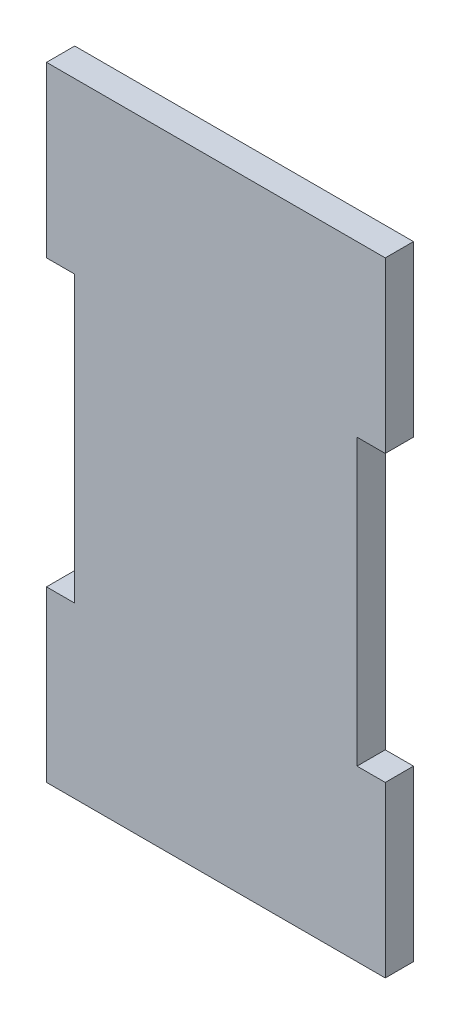
SolidWorks part; units mm, degrees
ref_plane "Front Plane" through (0, 0, 0) normal (0, 0, 1) x (1, 0, 0)
ref_plane "Top Plane" through (0, 0, 0) normal (0, 1, 0) x (1, 0, 0)
ref_plane "Right Plane" through (0, 0, 0) normal (1, 0, 0) x (0, 0, -1)
sketch "Sketch1" plane through (0, 0, 0) normal (0, 0, 1) x (1, 0, 0)
  line L0 (-3.175, 315.876) -> (-3.175, 296.826) construction
  line L1 (-38.1, 315.876) -> (0, 315.876)
  line L2 (-38.1, 315.876) -> (-38.1, 296.826)
  line L3 (-38.1, 245.7351) -> (0, 245.7351)
  line L4 (0, 315.876) -> (0, 296.826)
  line L5 (0, 245.7351) -> (-3.175, 245.7351)
  line L6 (0, 245.7351) -> (0, 264.7851)
  line L7 (0, 264.7851) -> (-3.175, 264.7851)
  line L9 (-38.1, 245.7351) -> (-34.925, 245.7351)
  line L10 (-38.1, 245.7351) -> (-38.1, 264.7851)
  line L11 (-38.1, 264.7851) -> (-34.925, 264.7851)
  line L13 (0, 315.876) -> (-3.175, 315.876)
  line L14 (0, 315.876) -> (0, 296.826)
  line L15 (0, 296.826) -> (-3.175, 296.826)
  line L16 (0, 264.7851) -> (0, 245.7351)
  line L17 (0, 296.826) -> (-3.175, 296.826) construction
  line L18 (-34.925, 296.826) -> (-34.925, 264.7851)
  line L19 (-38.1, 315.876) -> (-34.925, 315.876)
  line L20 (-38.1, 315.876) -> (-38.1, 296.826)
  line L21 (-38.1, 296.826) -> (-34.925, 296.826)
  line L22 (-38.1, 264.7851) -> (-38.1, 245.7351)
  line L23 (-34.925, 264.7851) -> (-34.3602, 265.6419)
  line L24 (-3.175, 264.7851) -> (-3.175, 296.826)
extrude "Boss-Extrude1" add sketch "Sketch1" along normal blind 3.175
